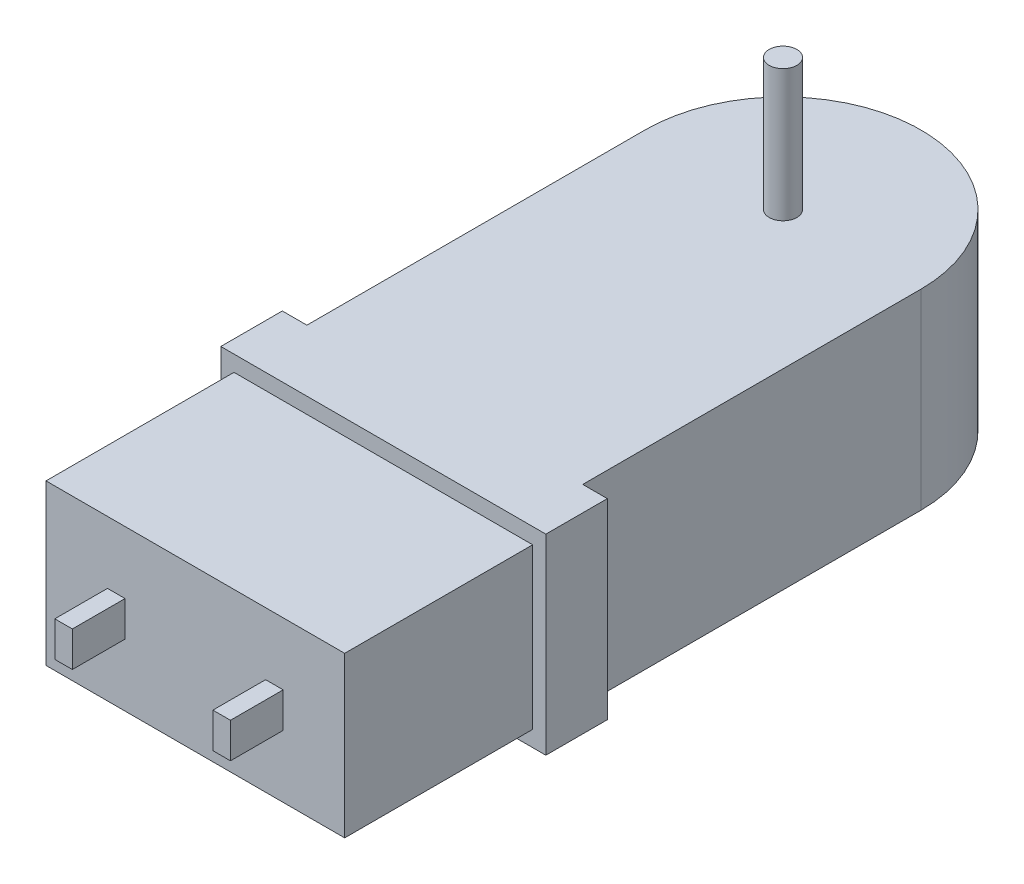
SolidWorks part; units mm, degrees
ref_plane "Front Plane" through (0, 0, 0) normal (0, 0, 1) x (1, 0, 0)
ref_plane "Top Plane" through (0, 0, 0) normal (0, 1, 0) x (1, 0, 0)
ref_plane "Right Plane" through (0, 0, 0) normal (1, 0, 0) x (0, 0, -1)
sketch "Sketch1" plane through (0, 0, 0) normal (0, 1, 0) x (1, 0, 0)
  line L1 (-9.9695, -24.4475) -> (-11.7475, -24.4475)
  line L2 (-11.7475, -24.4475) -> (-11.7475, -28.8925)
  line L3 (-9.9695, 0) -> (-9.9695, -24.4475)
  line L5 (9.9695, 0) -> (9.9695, -24.4475)
  line L6 (-11.7475, -28.8925) -> (-10.795, -28.8925)
  line L7 (-10.795, -28.8925) -> (-10.795, -42.4815)
  line L8 (-10.795, -42.4815) -> (10.795, -42.4815)
  line L9 (10.795, -28.8925) -> (10.795, -42.4815)
  line L10 (11.7475, -28.8925) -> (10.795, -28.8925)
  line L11 (11.7475, -24.4475) -> (11.7475, -28.8925)
  line L12 (9.9695, -24.4475) -> (11.7475, -24.4475)
  arc A0 (9.9695, 0) -> (-9.9695, 0) centre (0, 0) ccw
  point P13 (0, -42.4815)
  dimension "D1" = 52.451
  dimension "D2" = 19.939
  dimension "D3" = 23.495
  dimension "D4" = 21.59
  dimension "D5" = 4.445
  dimension "D6" = 13.589
extrude "Extrude1" add sketch "Sketch1" along normal mid plane 13.843
sketch "Sketch2" plane through (0, 0, 42.4815) normal (0, 0, 1) x (1, 0, 0)
  line L0 (11.7475, 6.9215) -> (11.7475, -6.9215) construction
  line L1 (-11.7475, 6.9215) -> (11.7475, 6.9215)
  line L2 (-11.7475, 6.9215) -> (-11.7475, 5.7785)
  line L3 (-11.7475, 5.7785) -> (11.7475, 5.7785)
  line L4 (11.7475, 6.9215) -> (11.7475, 5.7785)
  line L5 (-11.7475, 0) -> (11.7475, 0) construction
  line L6 (-11.7475, 6.9215) -> (-11.7475, -6.9215) construction
  line L7 (11.7475, -6.9215) -> (11.7475, -5.7785)
  line L8 (-11.7475, -5.7785) -> (11.7475, -5.7785)
  line L9 (-11.7475, -6.9215) -> (-11.7475, -5.7785)
  line L10 (-11.7475, -6.9215) -> (11.7475, -6.9215)
  dimension "D1" = 11.557
extrude "Cut-Extrude1" cut sketch "Sketch2" against normal up to surface (13.589 mm away) up to face at (-11.2713, 0, 28.8925)
sketch "Sketch3" plane through (0, 6.9215, 0) normal (0, 1, 0) x (1, 0, 0)
  circle A0 centre (0, 0) radius 1
  dimension "D1" = 2
extrude "Extrude2" add sketch "Sketch3" along normal blind 9.525 separate body
sketch "Sketch4" plane through (0, 0, 42.4815) normal (0, 0, 1) x (1, 0, 0)
  line L0 (-6.35, 0) -> (0, 0) construction
  line L1 (-6.35, 1.27) -> (-5.08, 1.27)
  line L2 (-6.35, 1.27) -> (-6.35, -1.27)
  line L3 (-6.35, -1.27) -> (-5.08, -1.27)
  line L4 (-5.08, 1.27) -> (-5.08, -1.27)
  line L5 (5.08, 1.27) -> (6.35, 1.27)
  line L6 (5.08, 1.27) -> (5.08, -1.27)
  line L7 (5.08, -1.27) -> (6.35, -1.27)
  line L8 (6.35, 1.27) -> (6.35, -1.27)
  line L9 (0, 0) -> (6.35, 0) construction
  dimension "D1" = 1.27
  dimension "D2" = 2.54
  dimension "D3" = 10.16
extrude "Extrude3" add sketch "Sketch4" along normal blind 3.81 separate body
